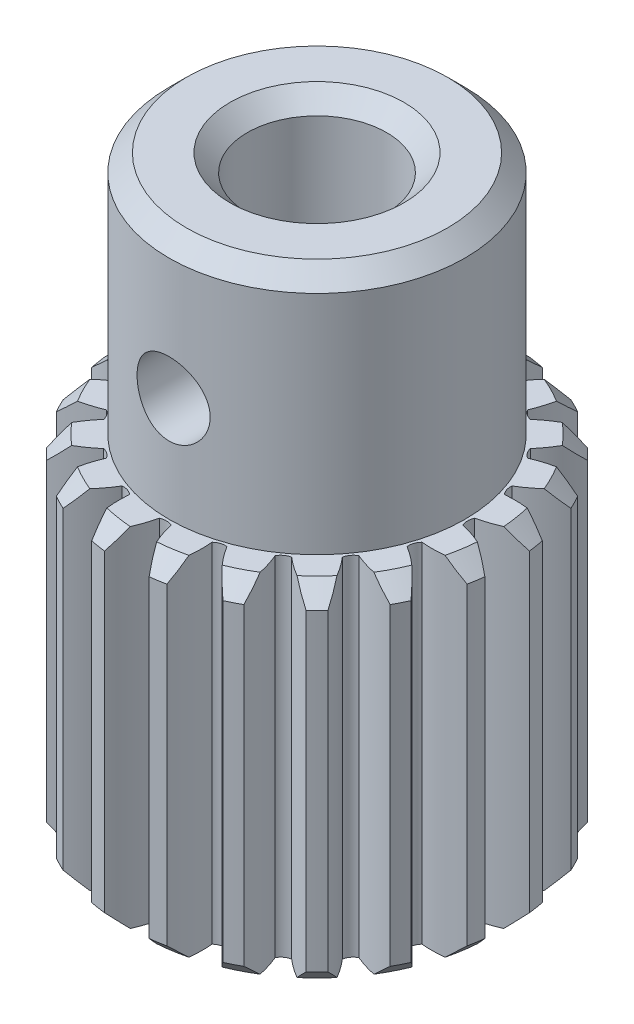
SolidWorks part; units mm, degrees
material "AISI 1045 鋼，冷拉"
ref_plane "Front Plane" through (0, 0, 0) normal (0, 0, 1) x (1, 0, 0)
ref_plane "Top Plane" through (0, 0, 0) normal (0, 1, 0) x (1, 0, 0)
ref_plane "Right Plane" through (0, 0, 0) normal (1, 0, 0) x (0, 0, -1)
sketch "草圖1" plane through (0, 0, 0) normal (0, 1, 0) x (1, 0, 0)
  circle A1 centre (0, 0) radius 11
  point P10 (0, 0)
  dimension "D1" = 40
  dimension "D2" = 22
  dimension "D3" = 37.5
  dimension "D4" = 110
  dimension "D5" = 4.5
extrude "填料-伸長1" add sketch "草圖1" along normal blind 20
sketch "草圖2" plane through (0, 20, 0) normal (0, 1, 0) x (1, 0, 0)
  line L3 (0, 0) -> (0, 11) construction
  arc A5 (-0.3393, 8.7188) -> (-1.2792, 10.9254) centre (-7.0051, 7.1829) ccw
  arc A6 (0.3393, 8.7188) -> (1.2792, 10.9254) centre (7.0051, 7.1829) cw
  arc A7 (1.2792, 10.9254) -> (-1.2792, 10.9254) centre (0, 0) ccw
  arc A8 (-0.3393, 8.7188) -> (0.3393, 8.7188) centre (0, 9.4872) ccw
  circle A17 centre (0, 0) radius 11 construction
  point P7 (0, 0)
  dimension "D1" = 1
  dimension "D2" = 0.84
  dimension "D4" = 2.5585
  dimension "D6" = 6.8404
  dimension "D3" = 7.9775
  dimension "D5" = 2.25
  dimension "D7" = 1.5128
extrude "除料-伸長1" cut sketch "草圖2" against normal through all
chamfer "導角1" distance 1 angle 45 2 edges at (0, 0, 11) (0, 20, 11)
pattern_circular "環狀複製排列1" count 20 over 360 about axis through (0, 0, 0) along (0, 1, 0) of "除料-伸長1"
sketch "草圖4" plane through (0, 20, 0) normal (0, 1, 0) x (1, 0, 0)
  circle A0 centre (0, 0) radius 8.5
  dimension "D1" = 17
extrude "填料-伸長2" add sketch "草圖4" along normal blind 14
sketch "草圖3" plane through (0, 0, 0) normal (0, -1, 0) x (1, 0, 0)
  circle A0 centre (0, 0) radius 4
  dimension "D1" = 8
extrude "除料-伸長2" cut sketch "草圖3" against normal through all
chamfer "導角3" distance 1 angle 45 1 edges at (0, 34, 8.5)
chamfer "導角2" distance 1 angle 45 2 edges at (0, 0, -4) (0, 34, -4)
hole_wizard "M5x0.8 螺紋孔1" positions "草圖6" profile "草圖7" tap size "M5x0.8" standard "Ansi Metric"
sketch "草圖6" plane through (0, 0, 0) normal (0, 0, 1) x (1, 0, 0)
  line L0 (0, 26) -> (0, 0) construction
  line L1 (7.5, 34) -> (-7.5, 34) construction
  point P0 (0, 26)
  dimension "D1" = 8
sketch "草圖7" plane through (0, 26, 0) normal (1, 0, 0) x (0, 1, 0)
  line L0 (0, 0) -> (0, 10.9254)
  line L1 (0, 10.9254) -> (2.1, 10.9254)
  line L2 (2.1, 10.9254) -> (2.1, 0)
  line L5 (2.1, 0) -> (0, 0)
  line L11 (0, -6.35) -> (0, 107.95) construction
  dimension "砮 脸ふ苝 畖" = 4.2
  dimension "砮 脸ふ苝瞏 " = 10.9254
pattern_circular "環狀複製排列2" count 2 over 90 about axis through (0, 34, 0) along (0, -1, 0) of "M5x0.8 螺紋孔1"
